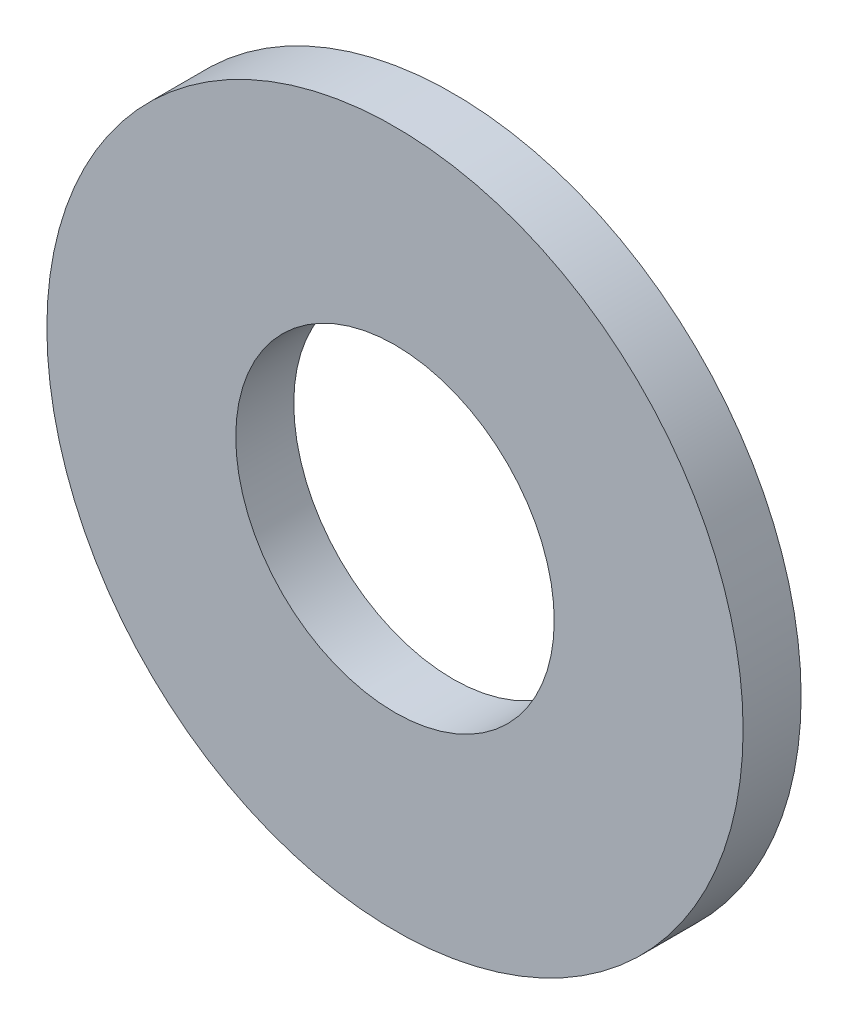
SolidWorks part; units mm, degrees
ref_plane "Front Plane" through (0, 0, 0) normal (0, 0, 1) x (1, 0, 0)
ref_plane "Top Plane" through (0, 0, 0) normal (0, 1, 0) x (1, 0, 0)
ref_plane "Right Plane" through (0, 0, 0) normal (1, 0, 0) x (0, 0, -1)
sketch "Sketch1" plane through (0, 0, 0) normal (0, 0, 1) x (1, 0, 0)
  circle A0 centre (-2.7953, -4.7007) radius 2.0583
  circle A1 centre (-2.7953, -4.7007) radius 4.5
  dimension "9" = 9
extrude "Boss-Extrude1" add sketch "Sketch1" along normal blind 0.75
